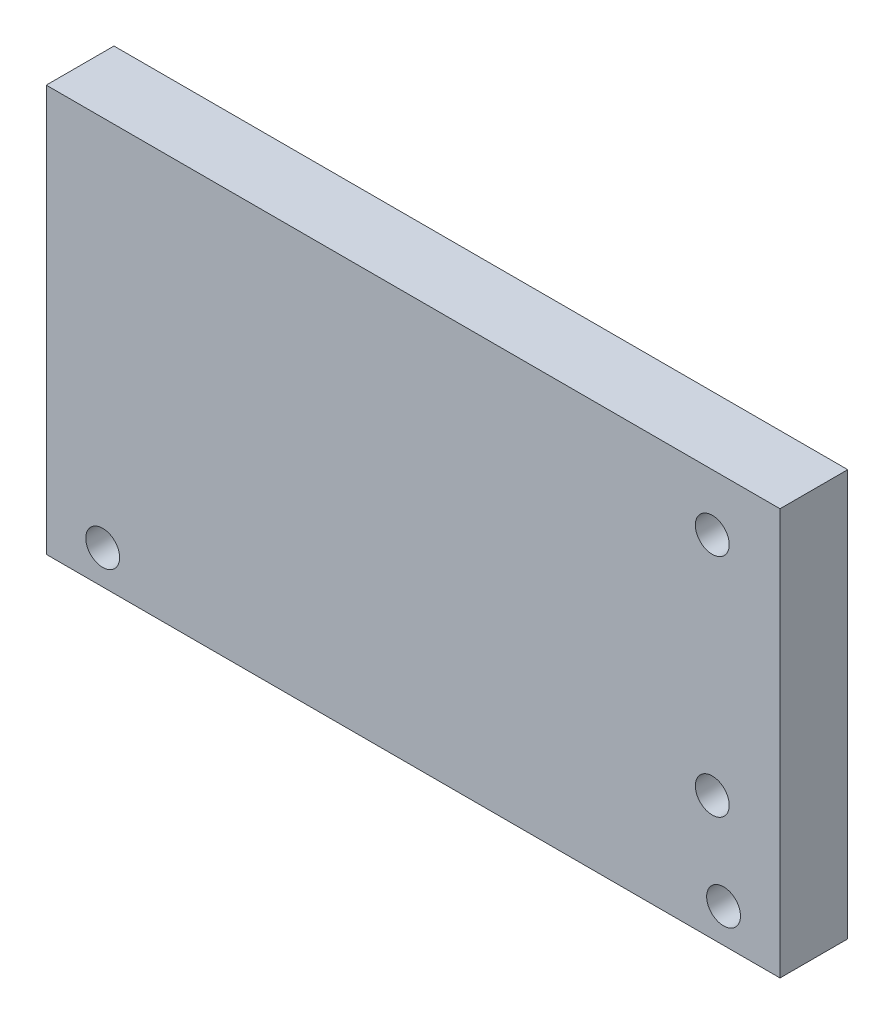
SolidWorks part; units mm, degrees
ref_plane "Plan de face" through (0, 0, 0) normal (0, 0, 1) x (1, 0, 0)
ref_plane "Plan de dessus" through (0, 0, 0) normal (0, 1, 0) x (1, 0, 0)
ref_plane "Plan de droite" through (0, 0, 0) normal (1, 0, 0) x (0, 0, -1)
sketch "Esquisse1" plane through (0, 0, 0) normal (0, 0, 1) x (1, 0, 0)
  line L1 (-40.2712, 36.6319) -> (24.7288, 36.6319)
  line L2 (-40.2712, 36.6319) -> (-40.2712, 0.6319)
  line L3 (-40.2712, 0.6319) -> (24.7288, 0.6319)
  line L4 (24.7288, 36.6319) -> (24.7288, 0.6319)
  circle A0 centre (18.7288, 31.6319) radius 1.5
  circle A1 centre (18.7288, 11.6319) radius 1.5
  dimension "D7" = 3
  dimension "D8" = 3
  dimension "D1" = 65
  dimension "D2" = 36
  dimension "D3" = 5
  dimension "D4" = 25
  dimension "D5" = 6
  dimension "D6" = 6
extrude "Boss.-Extru.1" add sketch "Esquisse1" along normal blind 6
sketch "Esquisse3" plane through (0, 0, 6) normal (0, 0, 1) x (1, 0, 0)
  line L0 (-40.2712, 0.6319) -> (24.7288, 0.6319) construction
  line L2 (24.7288, 0.6319) -> (24.7288, 36.6319) construction
  line L3 (-40.2712, 36.6319) -> (-40.2712, 0.6319) construction
  circle A0 centre (-35.2712, 3.6319) radius 1.5
  circle A1 centre (19.7288, 3.6319) radius 1.5
  dimension "D1" = 3
  dimension "D2" = 3
  dimension "D3" = 5
  dimension "D4" = 3
  dimension "D5" = 5
extrude "Enlèv. mat.-Extru.1" cut sketch "Esquisse3" against normal blind 10
